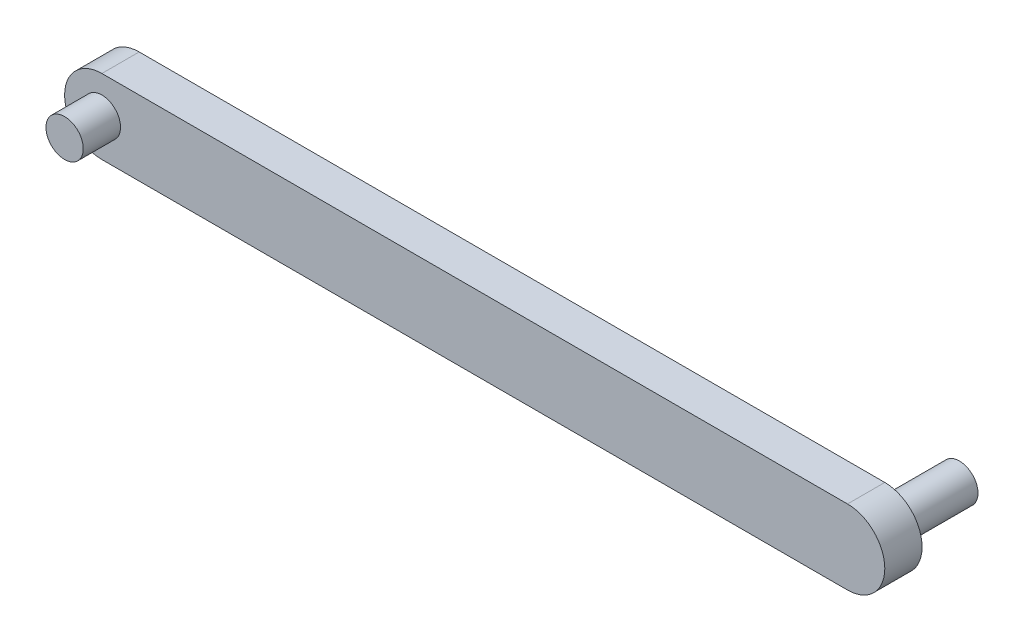
SolidWorks part; units mm, degrees
ref_plane "前视基准面" through (0, 0, 0) normal (0, 0, 1) x (1, 0, 0)
ref_plane "上视基准面" through (0, 0, 0) normal (0, 1, 0) x (1, 0, 0)
ref_plane "右视基准面" through (0, 0, 0) normal (1, 0, 0) x (0, 0, -1)
sketch "草图1" plane through (0, 0, 0) normal (0, 0, 1) x (1, 0, 0)
  line L1 (-33.6344, -4) -> (46.3656, -4)
  line L2 (-33.6344, 4) -> (46.3656, 4)
  arc A0 (46.3656, -4) -> (46.3656, 4) centre (46.3656, 0) ccw
  arc A1 (-33.6344, 4) -> (-33.6344, -4) centre (-33.6344, 0) ccw
  dimension "D1" = 80
extrude "凸台-拉伸1" add sketch "草图1" along normal blind 4
sketch "草图2" plane through (0, 0, 0) normal (0, 0, -1) x (-1, 0, 0)
  circle A1 centre (-46.3656, 0) radius 2
  dimension "D1" = 4
extrude "凸台-拉伸2" add sketch "草图2" along normal blind 8
sketch "草图3" plane through (0, 0, 4) normal (0, 0, 1) x (1, 0, 0)
  circle A1 centre (-33.6344, 0) radius 2
  dimension "D1" = 4
extrude "凸台-拉伸3" add sketch "草图3" along normal blind 4
